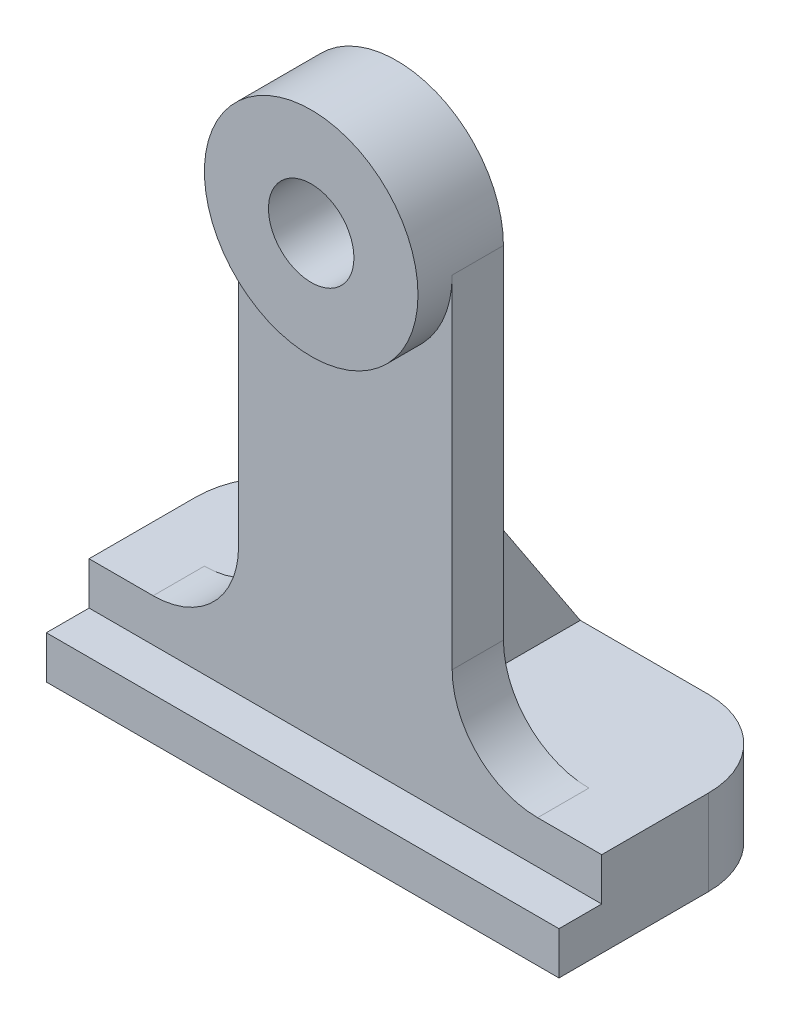
SolidWorks part; units mm, degrees
ref_plane "Front Plane" through (0, 0, 0) normal (0, 0, 1) x (1, 0, 0)
ref_plane "Top Plane" through (0, 0, 0) normal (0, 1, 0) x (1, 0, 0)
ref_plane "Right Plane" through (0, 0, 0) normal (1, 0, 0) x (0, 0, -1)
sketch "Sketch1" plane through (0, 0, 0) normal (0, 0, 1) x (1, 0, 0)
  line L0 (0, 0) -> (0, 0.3778) construction
  line L1 (0, 0.3778) -> (0, -0.4154) construction
  line L2 (0, 0) -> (0.5538, 0) construction
  line L3 (0.5538, 0) -> (-0.5094, 0) construction
  circle A0 centre (0, 0) radius 0.25
  circle A1 centre (0, 0) radius 0.625
  dimension "D1" = 0.5
  dimension "D2" = 1.25
extrude "Boss-Extrude1" add sketch "Sketch1" along normal blind 0.5
sketch "Sketch2" plane through (0, 0, 0) normal (0, 0, 1) x (1, 0, 0)
  line L0 (0, 0) -> (0, 0.5743) construction
  line L1 (0, 0.5743) -> (0, -0.4915) construction
  line L2 (0, 0) -> (-0.4606, 0) construction
  line L3 (-0.4606, 0) -> (0.399, 0) construction
  line L4 (0.625, 0) -> (0.625, -2.5)
  line L5 (0.625, -2.5) -> (-0.625, -2.5)
  line L6 (-0.625, -2.5) -> (-0.625, 0)
  line L7 (-0.625, 0) -> (0.625, 0)
  circle A0 centre (0, 0) radius 0.625 construction
  circle A1 centre (0, 0) radius 0.625 construction
  dimension "D1" = 2.5
extrude "Boss-Extrude2" add sketch "Sketch2" along normal blind 0.3
sketch "Sketch3" plane through (0, 0, 0.3) normal (0, 0, 1) x (1, 0, 0)
  line L0 (0, 0) -> (0, -2.9959) construction
  line L1 (0, -2.5) -> (-0.625, -2.5)
  line L2 (-0.625, -2.5) -> (0.625, -2.5) construction
  line L3 (-0.625, -2.5) -> (-1.5, -2.5)
  line L4 (-1.5, -2.5) -> (-1.5, -3)
  line L5 (-1.5, -3) -> (1.5, -3)
  line L6 (1.5, -3) -> (1.5, -2.5)
  line L7 (1.5, -2.5) -> (0.625, -2.5)
  line L8 (0.625, -2.5) -> (0, -2.5)
  dimension "D1" = 1.5
  dimension "D2" = 1.5
  dimension "D3" = 0.5
extrude "Boss-Extrude3" add sketch "Sketch3" against normal blind 1.125
sketch "Sketch4" plane through (0, 0, 0.3) normal (0, 0, 1) x (1, 0, 0)
  line L0 (1.5, -3) -> (1.5, -2.75)
  line L1 (1.5, -3) -> (1.5, -2.5) construction
  line L2 (1.5, -2.75) -> (-1.5, -2.75)
  line L3 (-1.5, -2.5) -> (-1.5, -3) construction
  line L4 (-1.5, -2.75) -> (-1.5, -3)
  line L5 (-1.5, -3) -> (1.5, -3)
  dimension "D1" = 0.25
extrude "Boss-Extrude4" add sketch "Sketch4" along normal blind 0.25
sketch "Sketch6" plane through (0, 0, 0.3) normal (0, 0, 1) x (1, 0, 0)
  circle A0 centre (0, 0) radius 0.25
extrude "Cut-Extrude1" cut sketch "Sketch6" against normal up to surface (0.3 mm away) up to face at (0, 0.125, 0)
fillet "Fillet1" radius 0.5 2 edges at (-0.625, -2.5, 0.15) (0.625, -2.5, 0.15)
sketch "Sketch7" plane through (0, 0, 0) normal (1, 0, 0) x (0, 0, -1)
  line L1 (0, -2) -> (0, 0) construction
  line L4 (0, -2.5) -> (0, -1.25)
  line L5 (0.825, -3) -> (-0.55, -3) construction
  line L6 (0, -1.25) -> (0.825, -2.5)
  line L7 (0.825, -2.5) -> (0, -2.5)
  dimension "D1" = 1.75
extrude "Boss-Extrude5" add sketch "Sketch7" along normal mid plane 0.5
sketch "Sketch8" plane through (0, -2.5, 0) normal (0, 1, 0) x (1, 0, 0)
  line L0 (1.5, -0.55) -> (-1.5, -0.55) construction
  point P0 (-1.0205, 0.33)
  point P1 (0.9795, 0.33)
  dimension "D1" = 0.88
  dimension "D2" = 0.88
  dimension "D3" = 2
fillet "Fillet2" radius 0.5 2 edges at (-1.5, -2.75, -0.825) (1.5, -2.75, -0.825)
